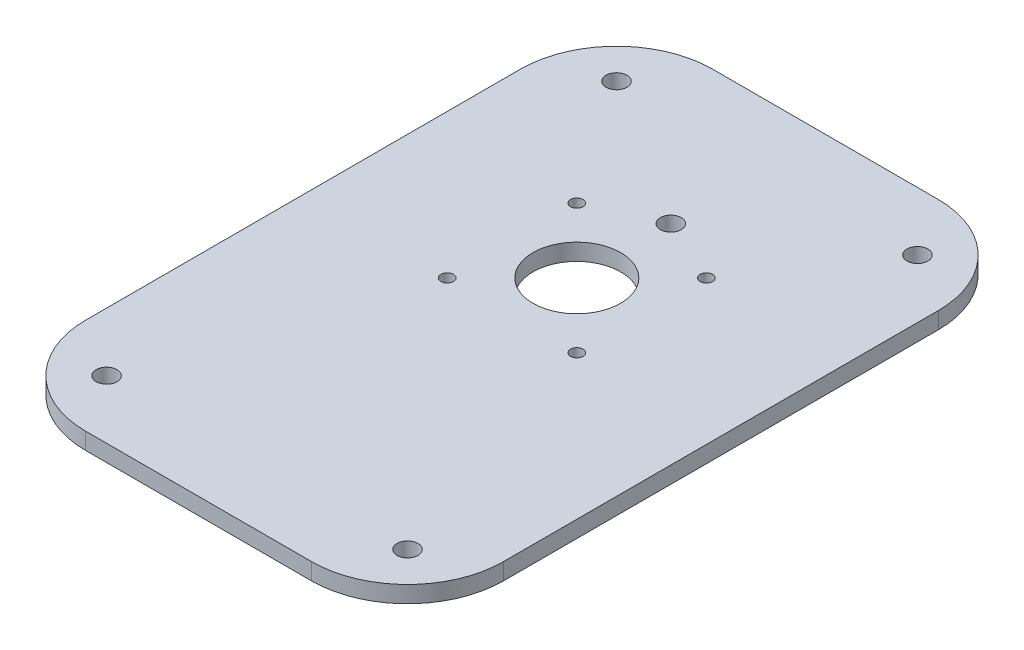
SolidWorks part; units mm, degrees
ref_plane "Front Plane" through (0, 0, 0) normal (0, 0, 1) x (1, 0, 0)
ref_plane "Top Plane" through (0, 0, 0) normal (0, 1, 0) x (1, 0, 0)
ref_plane "Right Plane" through (0, 0, 0) normal (1, 0, 0) x (0, 0, -1)
sketch "Sketch1" plane through (0, 0, 0) normal (0, 1, 0) x (1, 0, 0)
  line L0 (98.6595, -61) -> (-159.6366, -61) construction
  line L1 (-27, -75) -> (27, -75)
  line L2 (-50, -52) -> (-50, 52)
  line L3 (-27, 75) -> (27, 75)
  line L4 (50, -52) -> (50, 52)
  line L5 (-50, -75) -> (50, 75) construction
  line L6 (-50, 75) -> (50, -75) construction
  line L7 (-170.2562, 61) -> (110.7637, 61) construction
  line L8 (-36, 110.8385) -> (-36, -161.7345) construction
  line L9 (0, -145.8622) -> (0, 134.5406) construction
  line L11 (-15.5, 0) -> (15.5, 0) construction
  line L12 (-15.5, 0) -> (-15.5, 31) construction
  line L13 (-15.5, 31) -> (15.5, 31) construction
  line L14 (15.5, 0) -> (15.5, 31) construction
  line L15 (-15.5, 0) -> (15.5, 31) construction
  line L16 (-15.5, 31) -> (15.5, 0) construction
  arc A0 (-27, -75) -> (-50, -52) centre (-27, -52) cw
  arc A1 (27, -75) -> (50, -52) centre (27, -52) ccw
  arc A2 (27, 75) -> (50, 52) centre (27, 52) cw
  arc A3 (-50, 52) -> (-27, 75) centre (-27, 52) cw
  circle A4 centre (-36, 61) radius 2.5
  circle A5 centre (-36, -61) radius 2.5
  circle A6 centre (36, -61) radius 2.5
  circle A7 centre (36, 61) radius 2.5
  circle A8 centre (0, 38) radius 2.5
  circle A9 centre (0, 15.5) radius 10.5
  circle A10 centre (15.5, 31) radius 1.5
  circle A11 centre (-15.5, 31) radius 1.5
  circle A12 centre (-15.5, 0) radius 1.5
  circle A13 centre (15.5, 0) radius 1.5
  point P0 (0, 0)
  dimension "D3" = 23
  dimension "D7" = 5
  dimension "D9" = 5
  dimension "D11" = 21
  dimension "D14" = 3
  dimension "D1" = 150
  dimension "D2" = 100
  dimension "D4" = 14
  dimension "D5" = 14
  dimension "D6" = 14
  dimension "D8" = 113
  dimension "D10" = 22.5
  dimension "D12" = 31
  dimension "D13" = 31
extrude "Boss-Extrude1" add sketch "Sketch1" along normal blind 4
